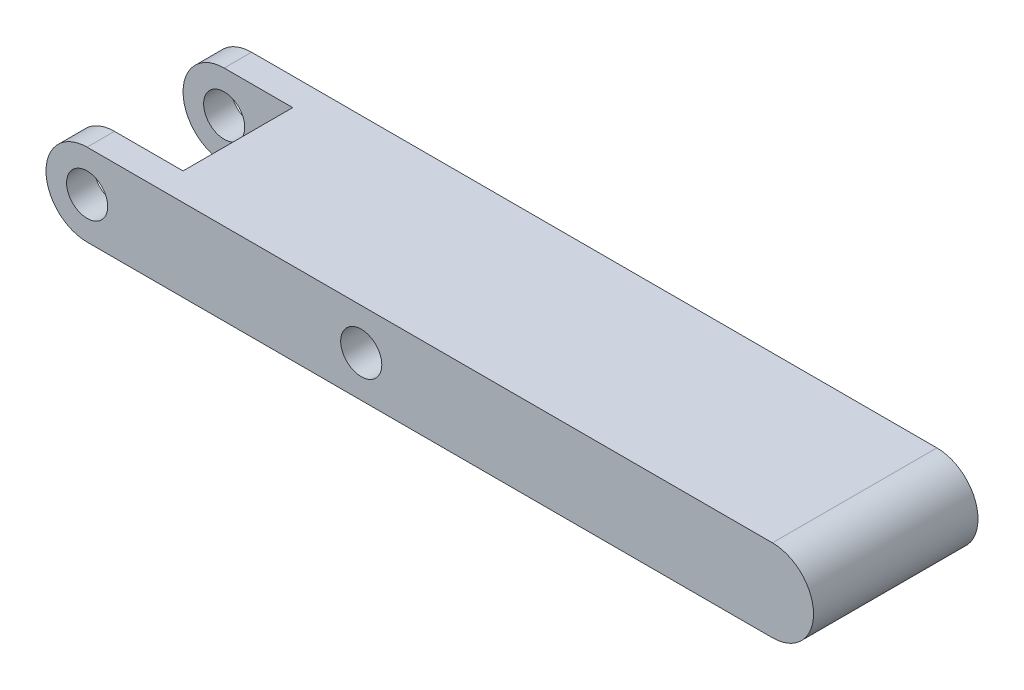
SolidWorks part; units mm, degrees
ref_plane "Front Plane" through (0, 0, 0) normal (0, 0, 1) x (1, 0, 0)
ref_plane "Top Plane" through (0, 0, 0) normal (0, 1, 0) x (1, 0, 0)
ref_plane "Right Plane" through (0, 0, 0) normal (1, 0, 0) x (0, 0, -1)
sketch "Sketch1" plane through (0, 0, 0) normal (0, 0, 1) x (1, 0, 0)
  line L0 (-25, 0) -> (25, 0) construction
  line L1 (-25, 3) -> (25, 3)
  line L2 (-25, -3) -> (25, -3)
  arc A0 (-25, 3) -> (-25, -3) centre (-25, 0) ccw
  arc A1 (25, -3) -> (25, 3) centre (25, 0) ccw
  circle A2 centre (-25, 0) radius 1.5
  circle A4 centre (-5, 0) radius 1.5
  point P2 (0, 0)
  dimension "D1" = 3
  dimension "D2" = 20
  dimension "D4" = 3
  dimension "D3" = 50
extrude "Boss-Extrude1" add sketch "Sketch1" along normal blind 12
sketch "Sketch3" plane through (0, 3, 0) normal (0, 1, 0) x (1, 0, 0)
  line L1 (25, 0) -> (-25, 0) construction
  line L2 (-35.2635, -2) -> (-20, -2)
  line L3 (-35.2635, -2) -> (-35.2635, -10)
  line L4 (-35.2635, -10) -> (-20, -10)
  line L5 (-20, -2) -> (-20, -10)
  line L8 (-25, -12) -> (-25, 0) construction
  dimension "D1" = 8
  dimension "D2" = 2
  dimension "D3" = 5
extrude "Cut-Extrude1" cut sketch "Sketch3" against normal blind 10 contours L4 L5 L2 L3
